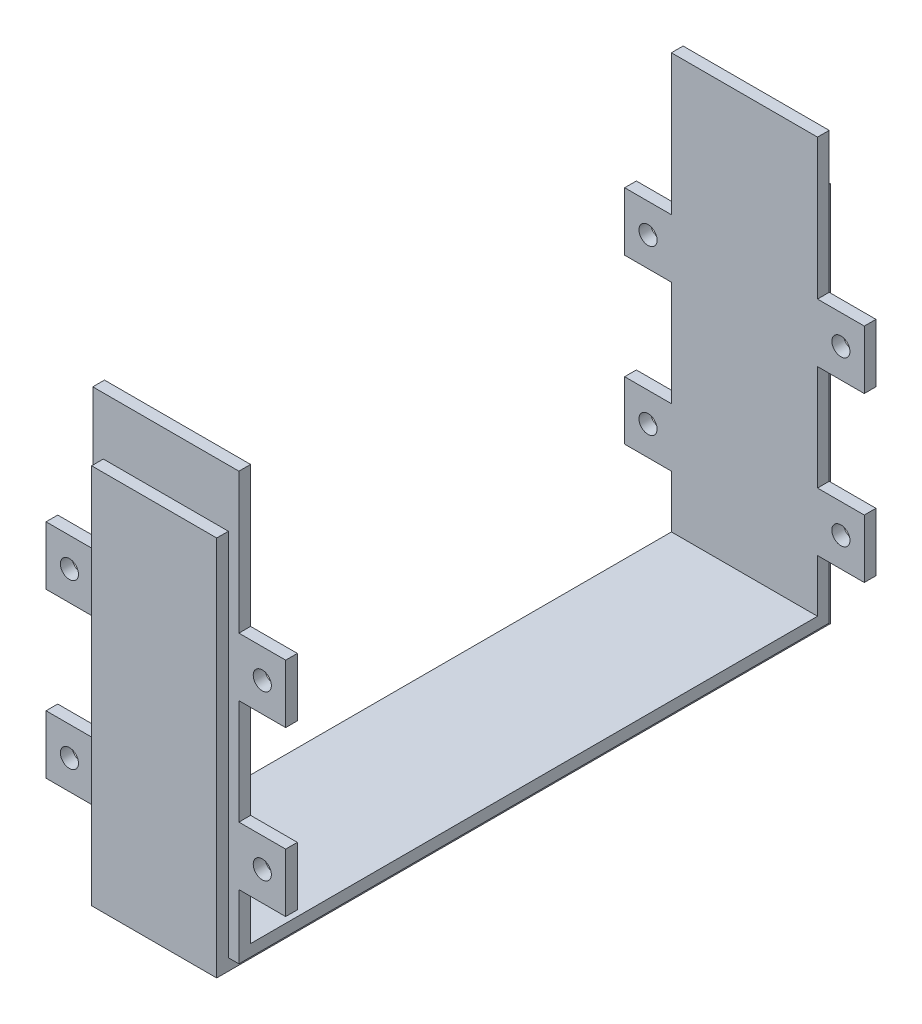
SolidWorks part; units mm, degrees
ref_plane "Front Plane" through (0, 0, 0) normal (0, 0, 1) x (1, 0, 0)
ref_plane "Top Plane" through (0, 0, 0) normal (0, 1, 0) x (1, 0, 0)
ref_plane "Right Plane" through (0, 0, 0) normal (1, 0, 0) x (0, 0, -1)
sketch "Sketch1" plane through (0, 0, 0) normal (1, 0, 0) x (0, 0, -1)
  line L1 (-52.5, 2) -> (52.5, 2)
  line L2 (-52.5, 2) -> (-52.5, -2)
  line L3 (-52.5, -2) -> (52.5, -2)
  line L4 (52.5, 2) -> (52.5, -2)
  line L5 (-52.5, 2) -> (52.5, -2) construction
  line L6 (-52.5, -2) -> (52.5, 2) construction
  line L7 (-52.5, 2) -> (-48.5, 2)
  line L8 (-52.5, 2) -> (-52.5, 63.2)
  line L9 (-52.5, 63.2) -> (-48.5, 63.2)
  line L10 (-48.5, 2) -> (-48.5, 63.2)
  line L11 (-48.5, 63.2) -> (-50.5, 63.2)
  line L12 (-48.5, 63.2) -> (-48.5, 73)
  line L13 (-48.5, 73) -> (-50.5, 73)
  line L14 (-50.5, 63.2) -> (-50.5, 73)
  line L15 (52.5, 2) -> (48.5, 2)
  line L16 (52.5, 2) -> (52.5, 63.2)
  line L17 (52.5, 63.2) -> (48.5, 63.2)
  line L18 (48.5, 2) -> (48.5, 63.2)
  line L19 (48.5, 63.2) -> (50.5, 63.2)
  line L20 (48.5, 63.2) -> (48.5, 73)
  line L21 (48.5, 73) -> (50.5, 73)
  line L22 (50.5, 63.2) -> (50.5, 73)
  point P0 (0, 0)
  dimension "D1" = 105
  dimension "D2" = 4
  dimension "D3" = 4
  dimension "D4" = 61.2
  dimension "D5" = 9.8
  dimension "D6" = 2
  dimension "D7" = 4
  dimension "D8" = 61.2
  dimension "D9" = 2
  dimension "D10" = 9.8
extrude "Boss-Extrude1" add sketch "Sketch1" along normal mid plane 25 contours L4 L1 L2 L3 | L1 L10 L9 L8 | L18 L1 L16 L17 | L12 L11 L14 L13 | L20 L19 L22 L21
sketch "Sketch2" plane through (0, 0, -48.5) normal (0, 0, 1) x (1, 0, 0)
  line L0 (-12.5, 2) -> (-12.5, 73) construction
  line L1 (-12.5, 11) -> (-20.5, 11)
  line L2 (-12.5, 11) -> (-12.5, 21)
  line L3 (-12.5, 21) -> (-20.5, 21)
  line L4 (-20.5, 11) -> (-20.5, 21)
  line L5 (12.5, 2) -> (-12.5, 2) construction
  line L6 (0, 73) -> (0, 13.7024) construction
  line L7 (-12.5, 39) -> (-20.5, 39)
  line L8 (-12.5, 39) -> (-12.5, 49)
  line L9 (-12.5, 49) -> (-20.5, 49)
  line L10 (-20.5, 39) -> (-20.5, 49)
  line L11 (12.5, 73) -> (-12.5, 73) construction
  line L12 (12.5, 21) -> (20.5, 21)
  line L13 (20.5, 11) -> (20.5, 21)
  line L14 (12.5, 11) -> (20.5, 11)
  line L15 (12.5, 11) -> (12.5, 21)
  line L16 (12.5, 49) -> (20.5, 49)
  line L17 (20.5, 39) -> (20.5, 49)
  line L18 (12.5, 39) -> (20.5, 39)
  line L19 (12.5, 39) -> (12.5, 49)
  circle A0 centre (-16.5, 44) radius 1.55
  circle A1 centre (-16.5, 16) radius 1.55
  circle A2 centre (16.5, 16) radius 1.55
  circle A3 centre (16.5, 44) radius 1.55
  dimension "D7" = 3.1
  dimension "D8" = 3.1
  dimension "D1" = 10
  dimension "D2" = 8
  dimension "D3" = 9
  dimension "D4" = 10
  dimension "D5" = 8
  dimension "D6" = 18
extrude "Boss-Extrude2" add sketch "Sketch2" against normal blind 2
sketch "Sketch4" plane through (0, 0, 48.5) normal (0, 0, -1) x (-1, 0, 0)
  line L0 (-12.5, 2) -> (-12.5, 73) construction
  line L1 (-12.5, 11) -> (-20.5, 11)
  line L2 (-12.5, 11) -> (-12.5, 21)
  line L3 (-12.5, 21) -> (-20.5, 21)
  line L4 (-20.5, 11) -> (-20.5, 21)
  line L5 (-12.5, 2) -> (12.5, 2) construction
  line L6 (0, 73) -> (0, 7.87) construction
  line L7 (-12.5, 39) -> (-20.5, 39)
  line L8 (-12.5, 39) -> (-12.5, 49)
  line L9 (-12.5, 49) -> (-20.5, 49)
  line L10 (-20.5, 39) -> (-20.5, 49)
  line L11 (-12.5, 73) -> (12.5, 73) construction
  line L12 (12.5, 21) -> (20.5, 21)
  line L13 (20.5, 11) -> (20.5, 21)
  line L14 (12.5, 11) -> (20.5, 11)
  line L15 (12.5, 11) -> (12.5, 21)
  line L16 (12.5, 49) -> (20.5, 49)
  line L17 (20.5, 39) -> (20.5, 49)
  line L18 (12.5, 39) -> (20.5, 39)
  line L19 (12.5, 39) -> (12.5, 49)
  circle A0 centre (-16.5, 44) radius 1.55
  circle A1 centre (-16.5, 16) radius 1.55
  circle A2 centre (16.5, 16) radius 1.55
  circle A3 centre (16.5, 44) radius 1.55
  dimension "D7" = 3.1
  dimension "D8" = 3.1
  dimension "D1" = 8
  dimension "D2" = 10
  dimension "D3" = 9
  dimension "D4" = 8
  dimension "D5" = 10
  dimension "D6" = 18
extrude "Boss-Extrude3" add sketch "Sketch4" against normal blind 2
sketch "Sketch5" plane through (-12.5, 0, 0) normal (-1, 0, 0) x (0, 0, 1)
  line L0 (52.5, -2) -> (-52.5, -2) construction
  line L1 (-52.5, 63.2) -> (-50.5, 63.2)
  line L2 (-52.5, 63.2) -> (-52.5, -2)
  line L3 (-52.5, -2) -> (-50.5, -2)
  line L4 (-50.5, 63.2) -> (-50.5, -2)
  line L6 (52.5, 63.2) -> (50.5, 63.2)
  line L7 (52.5, 63.2) -> (52.5, -2)
  line L8 (52.5, -2) -> (50.5, -2)
  line L9 (50.5, 63.2) -> (50.5, -2)
  line L10 (-50.5, -2) -> (50.5, -2)
  line L11 (-50.5, -2) -> (-50.5, 0)
  line L12 (-50.5, 0) -> (50.5, 0)
  line L13 (50.5, -2) -> (50.5, 0)
  line M7 (50.5, 49) -> (50.5, 39)
  line M11 (50.5, 21) -> (50.5, 11)
  line M17 (-50.5, 11) -> (-50.5, 21)
  line M21 (-50.5, 39) -> (-50.5, 49)
  line M26 (-50.5, 63.2) -> (-52.5, 63.2)
  line M27 (-52.5, 63.2) -> (-52.5, -2)
  line M28 (-52.5, -2) -> (52.5, -2)
  line M29 (52.5, -2) -> (52.5, 63.2)
  line M30 (52.5, 63.2) -> (50.5, 63.2)
  dimension "D1" = 2
  dimension "D2" = 2
  dimension "D3" = 2
extrude "Cut-Extrude1" cut sketch "Sketch5" against normal blind 1.8 contours L4 M26 M27 M28 M17 M21 | L12 L4 L9 M28 | L9 M30 M7 M11 M28 M29
sketch "Sketch6" plane through (12.5, 0, 0) normal (1, 0, 0) x (0, 0, -1)
  line L1 (-50.5, 63.2) -> (-52.5, 63.2)
  line L2 (-50.5, 63.2) -> (-50.5, -2)
  line L3 (-50.5, -2) -> (-52.5, -2)
  line L4 (-52.5, 63.2) -> (-52.5, -2)
  line L5 (50.5, 63.2) -> (52.5, 63.2)
  line L6 (50.5, 63.2) -> (50.5, -2)
  line L7 (50.5, -2) -> (52.5, -2)
  line L8 (52.5, 63.2) -> (52.5, -2)
  line L9 (-50.5, -2) -> (50.5, -2)
  line L10 (-50.5, -2) -> (-50.5, 0)
  line L11 (-50.5, 0) -> (50.5, 0)
  line L12 (50.5, -2) -> (50.5, 0)
  line M15 (-52.5, -2) -> (52.5, -2)
  dimension "D1" = 2
extrude "Cut-Extrude2" cut sketch "Sketch6" against normal blind 1.8 contours L11 L2 L6 M15
